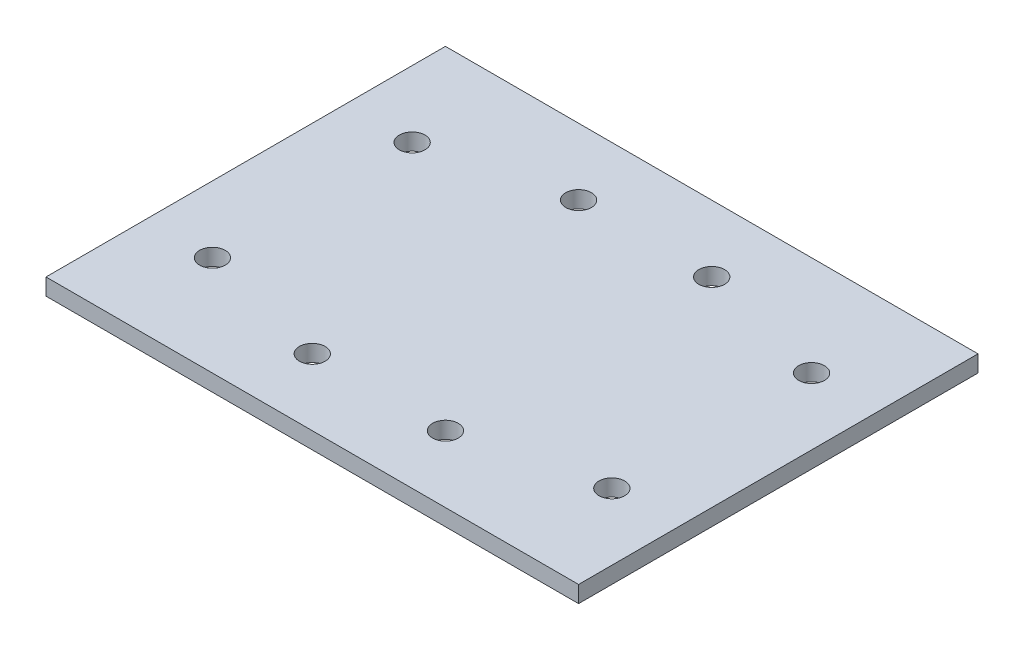
SolidWorks part; units mm, degrees
material "6061-T6 (SS)"
ref_plane "Front Plane" through (0, 0, 0) normal (0, 0, 1) x (1, 0, 0)
ref_plane "Top Plane" through (0, 0, 0) normal (0, 1, 0) x (1, 0, 0)
ref_plane "Right Plane" through (0, 0, 0) normal (1, 0, 0) x (0, 0, -1)
sketch "Sketch1" plane through (0, 0, 0) normal (0, 1, 0) x (1, 0, 0)
  line L1 (-101.6, -76.2) -> (101.6, -76.2)
  line L2 (-101.6, -76.2) -> (-101.6, 76.2)
  line L3 (-101.6, 76.2) -> (101.6, 76.2)
  line L4 (101.6, -76.2) -> (101.6, 76.2)
  line L5 (-101.6, -76.2) -> (101.6, 76.2) construction
  line L6 (-101.6, 76.2) -> (101.6, -76.2) construction
  point P0 (0, 0)
  dimension "D1" = 152.4
  dimension "D2" = 203.2
extrude "Boss-Extrude1" add sketch "Sketch1" along normal blind 6.35
hole_wizard "3/8 Clearance Hole1" positions "Sketch3" profile "Sketch2" hole size "3/8" standard "ANSI Inch" end condition through all
sketch "Sketch3" plane through (0, 6.35, 0) normal (0, 1, 0) x (1, 0, 0)
  line L0 (-76.2, 38.1) -> (76.2, 38.1) construction
  line L1 (76.2, 38.1) -> (76.2, -38.1) construction
  line L2 (-25.4, 50.8) -> (25.4, 50.8) construction
  line L4 (-25.4, -50.8) -> (25.4, -50.8) construction
  line L5 (101.6, 76.2) -> (-101.6, 76.2) construction
  line L6 (-101.6, -76.2) -> (101.6, -76.2) construction
  point P0 (-76.2, 38.1)
  point P2 (76.2, 38.1)
  point P4 (76.2, -38.1)
  point P6 (-76.2, -38.1)
  point P15 (0, 38.1)
  point P17 (76.2, 0)
  point P18 (-25.4, 50.8)
  point P20 (25.4, 50.8)
  point P22 (-25.4, -50.8)
  point P24 (25.4, -50.8)
  point P35 (0, 50.8)
  point P36 (0, -50.8)
  dimension "D1" = 152.4
  dimension "D2" = 76.2
  dimension "D3" = 50.8
  dimension "D4" = 50.8
  dimension "D5" = 25.4
  dimension "D6" = 25.4
sketch "Sketch2" plane through (-76.2, 6.35, -38.1) normal (1, 0, 0) x (0, 0, 1)
  line L0 (0, 0) -> (0, 6.35)
  line L1 (0, 6.35) -> (4.9022, 6.35)
  line L2 (4.9022, 6.35) -> (4.9022, 0)
  line L5 (4.9022, 0) -> (0, 0)
  line L11 (0, -6.35) -> (0, 107.95) construction
  dimension "Thru Hole Dia." = 9.8044
  dimension "Thru Hole Depth" = 6.35
